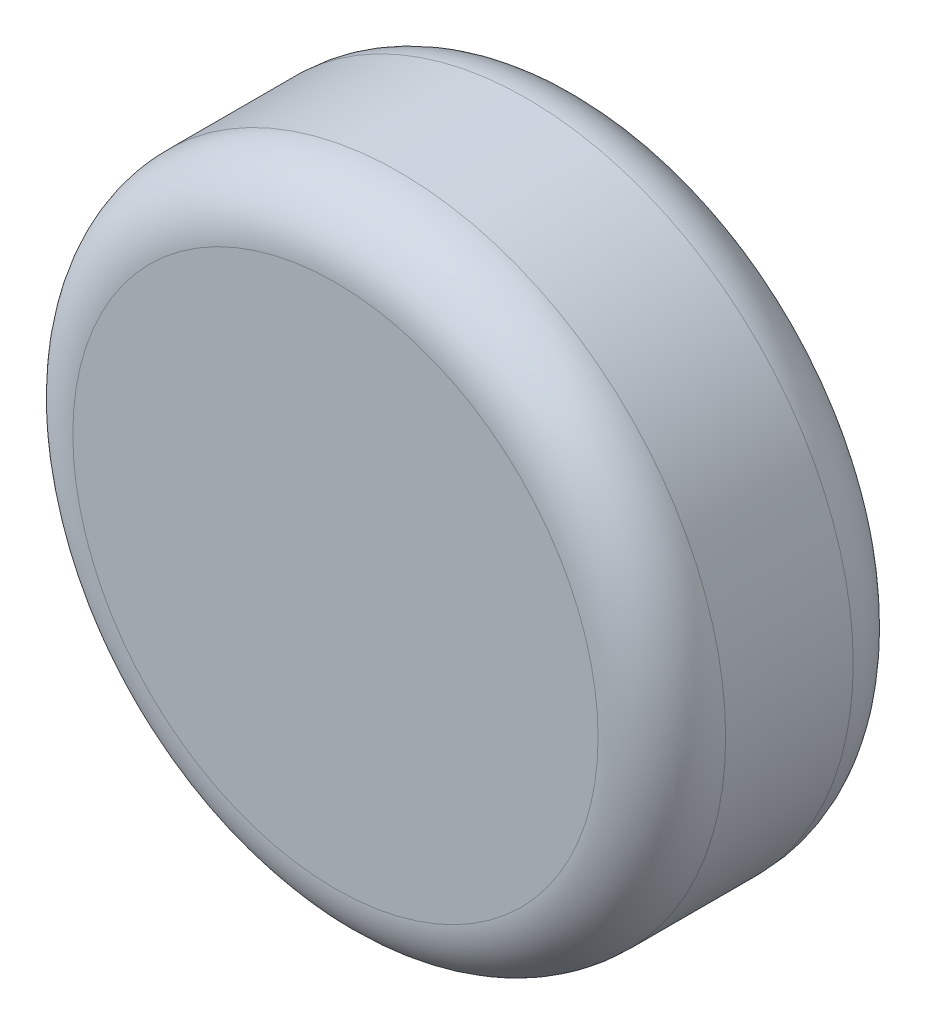
SolidWorks part; units mm, degrees
material "Delrin Sheet"
ref_plane "Front Plane" through (0, 0, 0) normal (0, 0, 1) x (1, 0, 0)
ref_plane "Top Plane" through (0, 0, 0) normal (0, 1, 0) x (1, 0, 0)
ref_plane "Right Plane" through (0, 0, 0) normal (1, 0, 0) x (0, 0, -1)
other "Bounding Box"
ref_plane "Default Plane" through (13.8565, 3.175, 6.7999) normal (0, -1, 0) x (-1, 0, 0)
sketch "Sketch1" plane through (0, 0, 0) normal (0, 0, 1) x (1, 0, 0)
  circle A0 centre (0, 0) radius 32.5
  dimension "D1" = 65
extrude "Boss-Extrude1" add sketch "Sketch1" along normal blind 25.4
fillet "Fillet1" radius 6.35 2 edges at (32.5, 0, 0) (32.5, 0, 25.4)
sketch "Sketch2" plane through (0, 0, 0) normal (0, 0, -1) x (-1, 0, 0)
  line L1 (3.4641, -6) -> (6.9282, 0)
  line L2 (6.9282, 0) -> (3.4641, 6)
  line L3 (3.4641, 6) -> (-3.4641, 6)
  line L4 (-3.4641, 6) -> (-6.9282, 0)
  line L5 (-6.9282, 0) -> (-3.4641, -6)
  line L6 (-3.4641, -6) -> (3.4641, -6)
  circle A0 centre (0, 0) radius 6 construction
  dimension "D1" = 12
extrude "Cut-Extrude1" cut sketch "Sketch2" against normal blind 15.621
